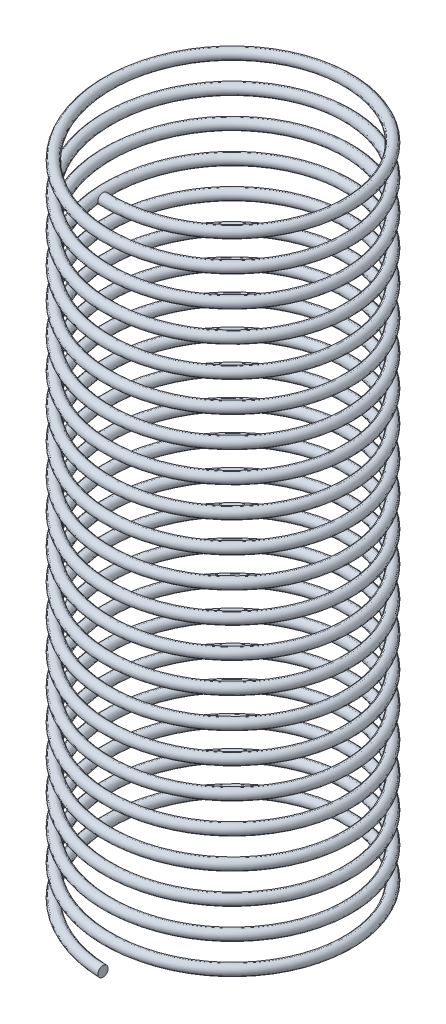
SolidWorks part; units mm, degrees
ref_plane "Front Plane" through (0, 0, 0) normal (0, 0, 1) x (1, 0, 0)
ref_plane "Top Plane" through (0, 0, 0) normal (0, 1, 0) x (1, 0, 0)
ref_plane "Right Plane" through (0, 0, 0) normal (1, 0, 0) x (0, 0, -1)
sketch "Sketch1" plane through (0, 0, 0) normal (0, 1, 0) x (1, 0, 0)
  circle A0 centre (0, 0) radius 2.985
  dimension "D1" = 5.97
curve "Helix/Spiral1" pitch 0.75 height 16.5 turns 22
sketch "Sketch2" plane through (0, 0, 0) normal (1, 0, 0) x (0, 0, -1)
  line L0 (3.369, 0) -> (-3.369, 0) construction
  circle A0 centre (-2.9575, 0) radius 0.1267
sweep "Sweep1" add profiles "Sketch2" path "Helix/Spiral1"
